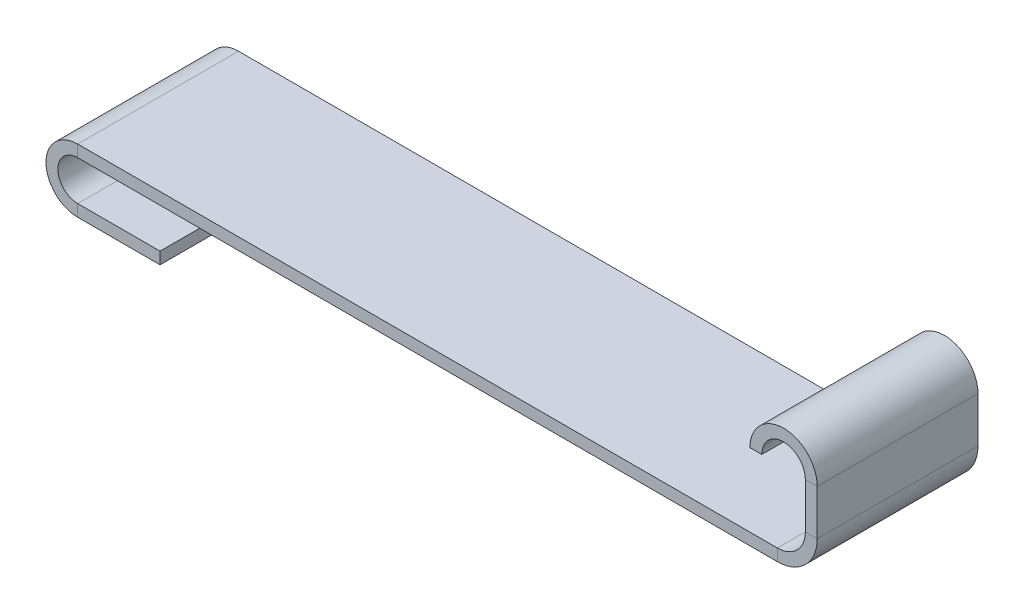
SolidWorks part; units mm, degrees
ref_plane "Front Plane" through (0, 0, 0) normal (0, 0, 1) x (1, 0, 0)
ref_plane "Top Plane" through (0, 0, 0) normal (0, 1, 0) x (1, 0, 0)
ref_plane "Right Plane" through (0, 0, 0) normal (1, 0, 0) x (0, 0, -1)
sketch "Sketch1" plane through (0, 0, 0) normal (0, 0, 1) x (1, 0, 0)
  line L0 (121.397, -136.1724) -> (121.397, -147.1724)
  line L1 (113.397, -155.1724) -> (-56.603, -155.1724)
  line L2 (-56.603, -168.1724) -> (-36.603, -168.1724)
  arc A0 (108.397, -136.1724) -> (121.397, -136.1724) centre (114.897, -136.1724) cw
  arc A1 (121.397, -147.1724) -> (113.397, -155.1724) centre (113.397, -147.1724) cw
  arc A2 (-56.603, -155.1724) -> (-56.603, -168.1724) centre (-56.603, -161.6724) ccw
  dimension "D1" = 13
  dimension "D6" = 8
  dimension "D2" = 19
  dimension "D3" = 13
  dimension "D4" = 170
  dimension "D5" = 20
ref_plane "Plane1" through (108.397, -136.1724, 0) normal (0, -1, 0) x (-1, 0, 0)
sketch "Sketch3" plane through (108.397, -136.1724, 0) normal (0, -1, 0) x (-1, 0, 0)
  line L0 (-1.2112, 19.5335) -> (-1.2112, -19.5335)
  line L3 (-1.2112, -19.5335) -> (1.6748, -19.5335)
  line L5 (1.6748, -19.5335) -> (1.6748, 19.5335)
  line L6 (1.6748, 19.5335) -> (-1.2112, 19.5335)
  line L7 (-13, 0) -> (0, 0) construction
  point P3 (-1.2112, 0)
sweep "Sweep2" add profiles "Sketch3" path "Sketch1"
